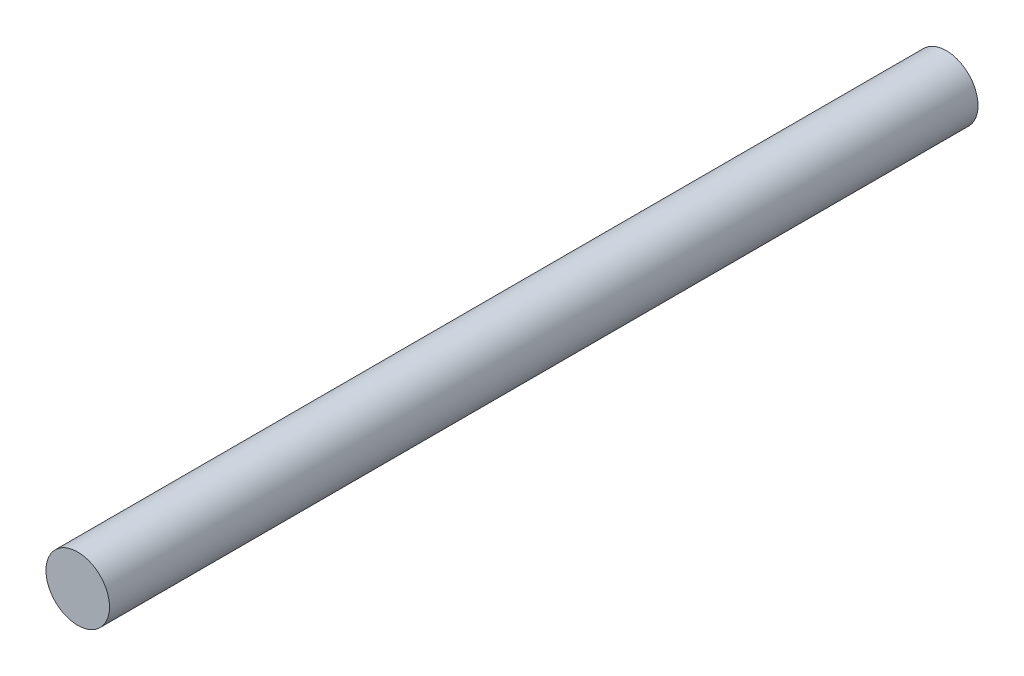
SolidWorks part; units mm, degrees
ref_plane "Front Plane" through (0, 0, 0) normal (0, 0, 1) x (1, 0, 0)
ref_plane "Top Plane" through (0, 0, 0) normal (0, 1, 0) x (1, 0, 0)
ref_plane "Right Plane" through (0, 0, 0) normal (1, 0, 0) x (0, 0, -1)
sketch "Sketch1" plane through (0, 0, 0) normal (0, 0, 1) x (1, 0, 0)
  circle A0 centre (0, 0) radius 3
  dimension "D1" = 6
extrude "Boss-Extrude1" add sketch "Sketch1" along normal blind 82
